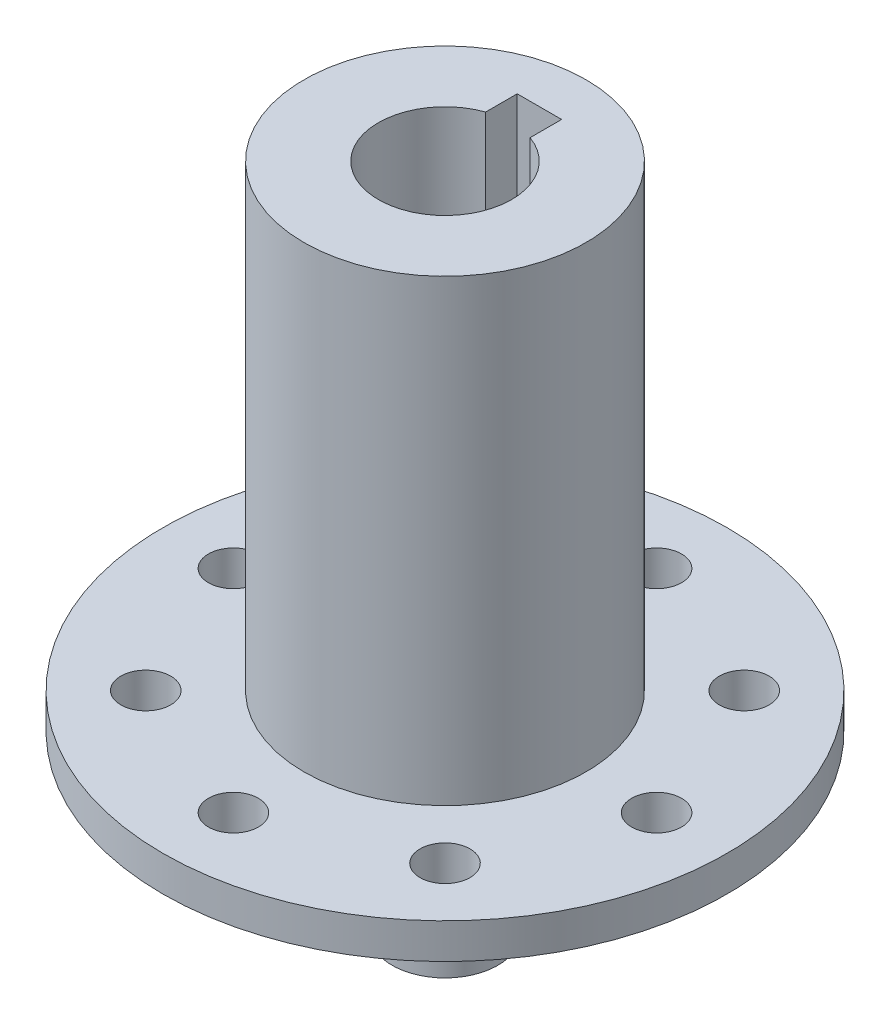
SolidWorks part; units mm, degrees
material "6061-T6 (SS)"
ref_plane "Front Plane" through (0, 0, 0) normal (0, 0, 1) x (1, 0, 0)
ref_plane "Top Plane" through (0, 0, 0) normal (0, 1, 0) x (1, 0, 0)
ref_plane "Right Plane" through (0, 0, 0) normal (1, 0, 0) x (0, 0, -1)
sketch "Sketch1" plane through (0, 0, 0) normal (0, 1, 0) x (1, 0, 0)
  line L0 (-2, 5.6569) -> (-2, 8.5) construction
  line L1 (-2, 8.5) -> (2, 8.5) construction
  line L3 (-2, 3.5) -> (2, 3.5) construction
  line L5 (2, 5.6569) -> (2, 8.5) construction
  circle A0 centre (0, 0) radius 22.225 construction
  circle A2 centre (0, 0) radius 12.7
  point P8 (0, 8.5)
  point P10 (0, -6)
  point P11 (-2, 5.6569)
  point P12 (2, 5.6569)
  dimension "D1" = 44.45
  dimension "D6" = 25.4
  dimension "D3" = 4
  dimension "D4" = 5
  dimension "D5" = 9.5
extrude "Boss-Extrude1" add sketch "Sketch1" along normal blind 41.275
sketch "Sketch2" plane through (0, 0, 0) normal (0, -1, 0) x (1, 0, 0)
  circle A0 centre (0, 0) radius 25.4
  circle A3 centre (0, 0) radius 12.7
  dimension "D1" = 50.8
  dimension "D2" = 25.4
sketch "Sketch3" plane through (0, 0, 0) normal (0, -1, 0) x (1, 0, 0)
  circle A1 centre (0, 0) radius 25.4
  point P4 (0, 0)
  dimension "D1" = 50.8
extrude "Boss-Extrude3" add sketch "Sketch3" along normal blind 3.175
sketch "Sketch4" plane through (0, -3.175, 0) normal (0, -1, 0) x (1, 0, 0)
  line L0 (0, 19.05) -> (0, -19.05) construction
  line L1 (19.05, 0) -> (-19.05, 0) construction
  line L2 (13.4704, 13.4704) -> (-13.4704, -13.4704) construction
  line L3 (-13.4704, 13.4704) -> (13.4704, -13.4704) construction
  point P6 (0, 0)
  point P7 (0, 0)
  point P10 (0, 0)
  point P13 (0, 0)
  dimension "D1" = 45
  dimension "D2" = 45
  dimension "D3" = 38.1
hole_wizard "#8 Clearance Hole1" positions "Sketch5" profile "Sketch6" hole size "#8" standard "ANSI Inch" end condition through all
sketch "Sketch5" plane through (0, -3.175, 0) normal (0, -1, 0) x (-1, 0, 0)
  point P0 (0, 19.05)
  point P3 (-13.4704, 13.4704)
  point P6 (-19.05, 0)
  point P9 (-13.4704, -13.4704)
  point P12 (0, -19.05)
  point P15 (13.4704, -13.4704)
  point P18 (19.05, 0)
  point P21 (13.4704, 13.4704)
sketch "Sketch6" plane through (0, -3.175, -19.05) normal (1, 0, 0) x (0, 0, -1)
  line L0 (0, 0) -> (0, 44.45)
  line L1 (0, 44.45) -> (2.2479, 44.45)
  line L2 (2.2479, 44.45) -> (2.2479, 0)
  line L5 (2.2479, 0) -> (0, 0)
  line L11 (0, -6.35) -> (0, 107.95) construction
  dimension "Thru Hole Dia." = 4.4958
  dimension "Thru Hole Depth" = 44.45
sketch "Sketch7" plane through (0, 41.275, 0) normal (0, 1, 0) x (1, 0, 0)
  line L0 (-2, 5.6569) -> (-2, 3.5) construction
  line L1 (-2, 8.5) -> (2, 8.5)
  line L2 (-2, 8.5) -> (-2, 5.6569)
  line L4 (2, 8.5) -> (2, 5.6569)
  line L5 (-2, 3.5) -> (2, 3.5) construction
  line L6 (2, 3.5) -> (2, 5.6569) construction
  arc A2 (-2, 5.6569) -> (2, 5.6569) centre (0, 0) ccw
  arc A3 (-2, 5.6569) -> (2, 5.6569) centre (0, 0) cw construction
  point P1 (0, 8.5)
  point P8 (0, -6)
  point P11 (0, 6)
  dimension "D4" = 12
  dimension "D1" = 14.5
  dimension "D2" = 9.5
  dimension "D3" = 4
  dimension "D5" = 2.5
extrude "20.8mmToEndofKeyway" cut sketch "Sketch7" against normal blind 25
sketch "Sketch8" plane through (0, -3.175, 0) normal (0, -1, 0) x (1, 0, 0)
  circle A0 centre (0, 0) radius 4.7625
  circle A2 centre (0, -19.05) radius 2.2479 construction
  circle A3 centre (0, -19.05) radius 2.2479 construction
  circle A4 centre (0, -19.05) radius 4.0894 construction
  dimension "D1" = 9.525
  dimension "D2" = 8.1788
extrude "Boss-Extrude4" add sketch "Sketch8" along normal blind 15.875
fillet "Fillet1" radius 5 1 edges at (0, -3.175, -4.7625)
